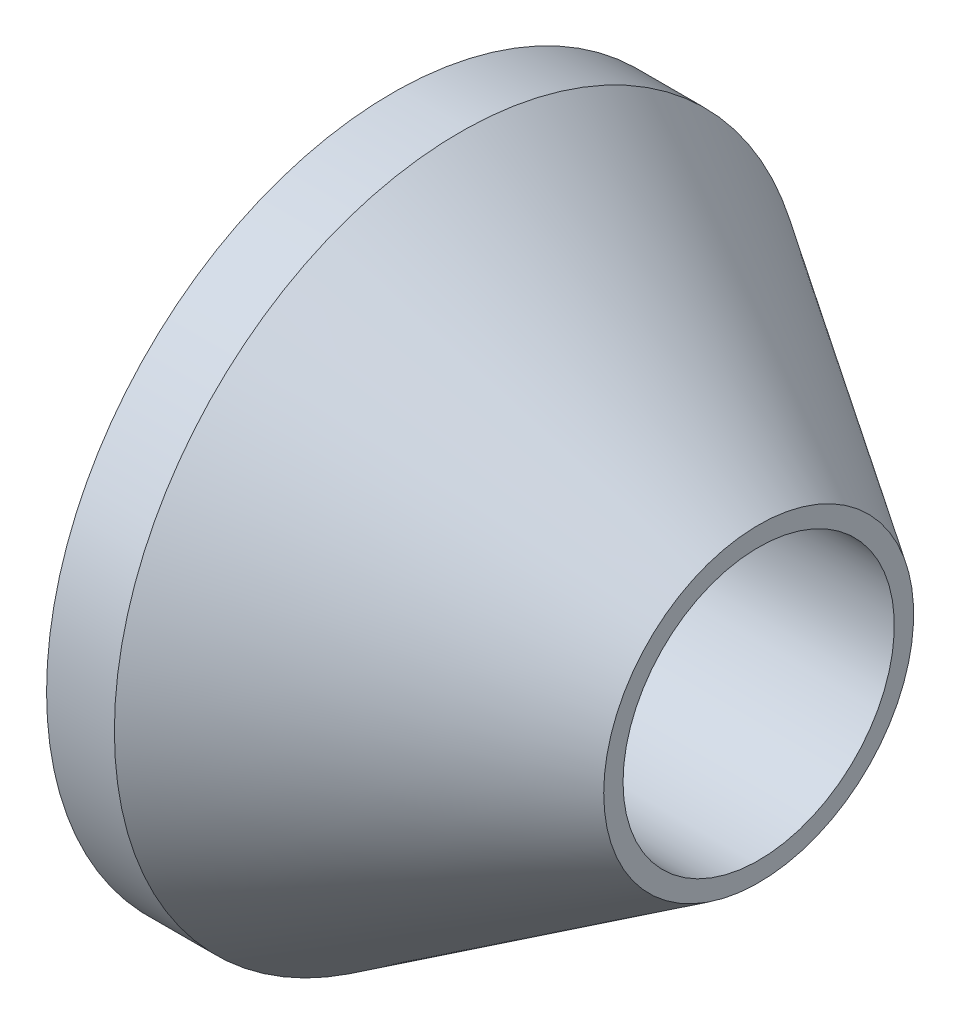
SolidWorks part; units mm, degrees
material "Glass"
ref_plane "Front Plane" through (0, 0, 0) normal (0, 0, 1) x (1, 0, 0)
ref_plane "Top Plane" through (0, 0, 0) normal (0, 1, 0) x (1, 0, 0)
ref_plane "Right Plane" through (0, 0, 0) normal (1, 0, 0) x (0, 0, -1)
sketch "Sketch1" plane through (0, 0, 0) normal (0, 1, 0) x (1, 0, 0)
  line L0 (-10.8, 10.2) -> (-10.8, 0)
  line L1 (0, 4) -> (-6, 4)
  line L2 (-10.8, 10.2) -> (-8.8, 10.2)
  line L3 (-6, 0) -> (14.0957, 0) construction
  line L4 (-6, 4) -> (-6, 0)
  line L5 (-8.8, 10.2) -> (0, 4.57)
  line L6 (0, 4.57) -> (0, 4)
  line L8 (-6, 0) -> (-10.8, 0)
  dimension "D1" = 4
  dimension "D2" = 10.8
  dimension "D3" = 6
  dimension "D4" = 10.2
  dimension "D5" = 4.57
  dimension "D7" = 2
revolve "Revolve2" add sketch "Sketch1" angle 360 about L3
